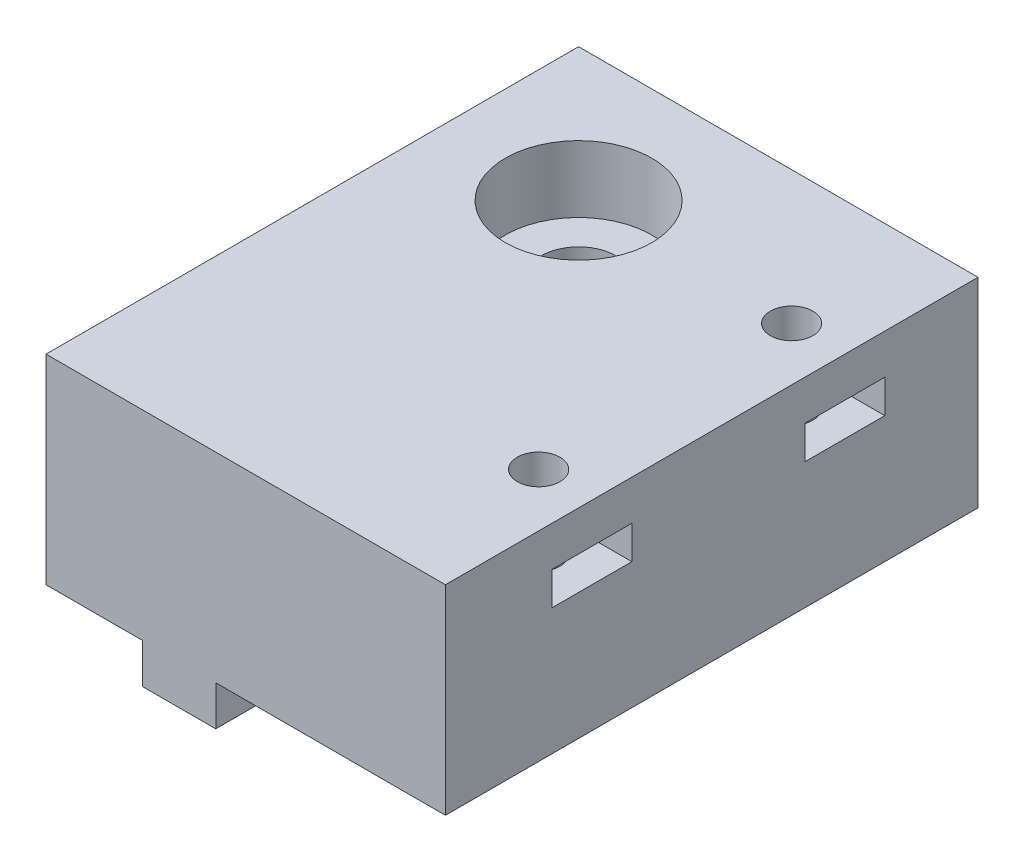
SolidWorks part; units mm, degrees
ref_plane "Front Plane" through (0, 0, 0) normal (0, 0, 1) x (1, 0, 0)
ref_plane "Top Plane" through (0, 0, 0) normal (0, 1, 0) x (1, 0, 0)
ref_plane "Right Plane" through (0, 0, 0) normal (1, 0, 0) x (0, 0, -1)
sketch "Sketch1" plane through (0, 0, 0) normal (0, 1, 0) x (1, 0, 0)
  line L1 (-0.6968, 0) -> (29.3032, 0)
  line L2 (-0.6968, 0) -> (-0.6968, 40)
  line L3 (-0.6968, 40) -> (29.3032, 40)
  line L4 (29.3032, 0) -> (29.3032, 40)
  dimension "D1" = 40
  dimension "D2" = 30
extrude "Boss-Extrude1" add sketch "Sketch1" along normal blind 15
sketch "Sketch5" plane through (0, 15, 0) normal (0, 1, 0) x (1, 0, 0)
  line L0 (29.3032, 0) -> (29.3032, 40) construction
  line L2 (29.3032, 40) -> (-0.6968, 40) construction
  circle A0 centre (25.3032, 11) radius 1.6
  circle A1 centre (25.3032, 30) radius 1.6
  dimension "D1" = 3.2
  dimension "D2" = 3.2
  dimension "D3" = 4
  dimension "D6" = 10
  dimension "D4" = 4
  dimension "D5" = 19
extrude "Cut-Extrude3" cut sketch "Sketch5" against normal through all
sketch "Sketch6" plane through (29.3032, 0, 0) normal (1, 0, 0) x (0, 0, -1)
  line L0 (0, 15) -> (40, 15) construction
  line L1 (8, 12) -> (14, 12)
  line L2 (8, 12) -> (8, 9.5)
  line L3 (8, 9.5) -> (14, 9.5)
  line L4 (14, 12) -> (14, 9.5)
  line L5 (27, 12) -> (33, 12)
  line L6 (27, 12) -> (27, 9.5)
  line L7 (27, 9.5) -> (33, 9.5)
  line L8 (33, 12) -> (33, 9.5)
  line L10 (40, 15) -> (40, 0) construction
  point P10 (33, 10.75)
  dimension "D1" = 2.5
  dimension "D2" = 6
  dimension "D3" = 2.5
  dimension "D4" = 6
  dimension "D5" = 7
  dimension "D6" = 19
  dimension "D7" = 3
  dimension "D8" = 3
extrude "Cut-Extrude4" cut sketch "Sketch6" against normal blind 8
sketch "Sketch10" plane through (0, 15, 0) normal (0, 1, 0) x (1, 0, 0)
  line L0 (29.3032, 40) -> (-0.6968, 40) construction
  line L1 (-0.6968, 40) -> (-0.6968, 0) construction
  circle A0 centre (9.3032, 30) radius 2.8
  dimension "D1" = 5.6
  dimension "D2" = 10
  dimension "D3" = 10
extrude "Cut-Extrude7" cut sketch "Sketch10" against normal through all
sketch "Sketch11" plane through (0, 15, 0) normal (0, 1, 0) x (1, 0, 0)
  circle A0 centre (9.3032, 30) radius 5.5
  dimension "D1" = 11
extrude "Cut-Extrude8" cut sketch "Sketch11" against normal blind 5
sketch "Sketch12" plane through (0, 0, 0) normal (0, -1, 0) x (1, 0, 0)
  line L0 (-0.6968, 0) -> (29.3032, 0) construction
  line L1 (6.5532, 0) -> (12.0532, 0)
  line L2 (6.5532, 0) -> (6.5532, -22.5)
  line L3 (6.5532, -40) -> (12.0532, -40)
  line L4 (12.0532, 0) -> (12.0532, -22.5)
  line L5 (29.3032, -40) -> (-0.6968, -40) construction
  line L6 (6.5532, -37.5) -> (6.5532, -40)
  line L7 (6.5532, -22.5) -> (12.0532, -22.5)
  line L9 (6.5532, -37.5) -> (12.0532, -37.5)
  line L11 (12.0532, -37.5) -> (12.0532, -40)
  circle A0 centre (9.3032, -30) radius 2.8 construction
  dimension "D2" = 2.75
  dimension "D1" = 5.5
  dimension "D3" = 15
  dimension "D4" = 7.5
extrude "Boss-Extrude7" add sketch "Sketch12" along normal blind 3
